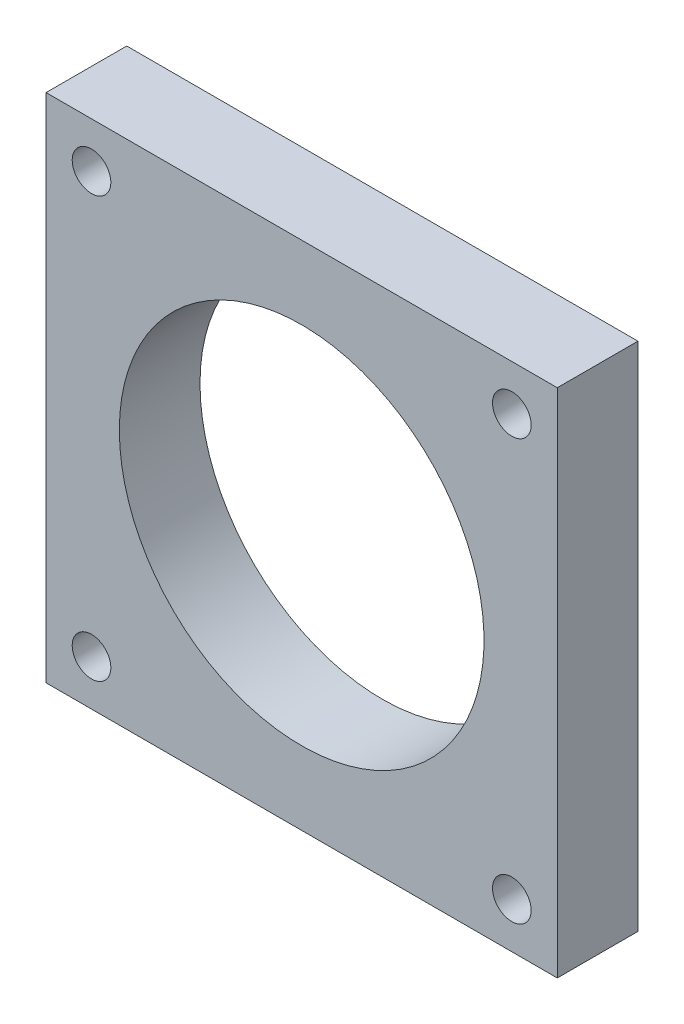
SolidWorks part; units mm, degrees
ref_plane "Front Plane" through (0, 0, 0) normal (0, 0, 1) x (1, 0, 0)
ref_plane "Top Plane" through (0, 0, 0) normal (0, 1, 0) x (1, 0, 0)
ref_plane "Right Plane" through (0, 0, 0) normal (1, 0, 0) x (0, 0, -1)
sketch "Sketch1" plane through (0, 0, 0) normal (0, 0, 1) x (1, 0, 0)
  line L1 (-22.5, -22.5) -> (22.5, -22.5)
  line L2 (-22.5, -22.5) -> (-22.5, 22.5)
  line L3 (-22.5, 22.5) -> (22.5, 22.5)
  line L4 (22.5, -22.5) -> (22.5, 22.5)
  line L5 (-22.5, -22.5) -> (22.5, 22.5) construction
  line L6 (-22.5, 22.5) -> (22.5, -22.5) construction
  circle A0 centre (0, 0) radius 16
  point P0 (0, 0)
  dimension "D3" = 32
  dimension "D1" = 45
  dimension "D2" = 45
extrude "Boss-Extrude1" add sketch "Sketch1" along normal blind 7.1
hole_wizard "M3x0.5 Tapped Hole1" positions "Sketch2" profile "Sketch3" tap size "M3x0.5" standard "ANSI Metric"
sketch "Sketch2" plane through (0, 0, 0) normal (0, 0, -1) x (-1, 0, 0)
  line L16 (-18.5, 18.5) -> (-18.5, -18.5)
  line L17 (-18.5, -18.5) -> (18.5, -18.5)
  line L18 (18.5, -18.5) -> (18.5, 18.5)
  line L19 (18.5, 18.5) -> (-18.5, 18.5)
  point P25 (-18.5, 18.5)
  point P26 (-18.5, -18.5)
  point P27 (18.5, -18.5)
  point P28 (18.5, 18.5)
sketch "Sketch3" plane through (18.5, 18.5, 0) normal (1, 0, 0) x (0, 1, 0)
  line L0 (0, 0) -> (0, 15.7511)
  line L1 (0, 15.7511) -> (1.25, 15)
  line L2 (1.25, 15) -> (1.25, 0)
  line L3 (1.25, 0) -> (0, 0)
  line L4 (0, 15.7511) -> (-1.25, 15) construction
  line L5 (0, -6.35) -> (0, 107.95) construction
  dimension "Tap Drill Dia." = 2.5
  dimension "Tap Drill Depth" = 15
  dimension "Drill Angle" = 118
cosmetic thread "Hole Thread1"
cosmetic thread "Hole Thread2"
cosmetic thread "Hole Thread3"
cosmetic thread "Hole Thread4"
hole_wizard "CBORE for M3 SHCS1" positions "Sketch4" profile "Sketch5" counterbore size "M3" standard "ANSI Metric"
sketch "Sketch4" plane through (0, 0, 0) normal (0, 0, -1) x (-1, 0, 0)
  point P0 (-18.5, 18.5)
  point P3 (18.5, 18.5)
  point P6 (18.5, -18.5)
  point P9 (-18.5, -18.5)
sketch "Sketch5" plane through (18.5, 18.5, 0) normal (1, 0, 0) x (0, 1, 0)
  line L0 (0, 0) -> (0, 8.1215)
  line L1 (0, 8.1215) -> (1.7, 7.1)
  line L2 (1.7, 7.1) -> (1.7, 3)
  line L3 (1.7, 3) -> (3.25, 3)
  line L4 (3.25, 3) -> (3.25, 0)
  line L5 (3.25, 0) -> (0, 0)
  line L6 (0, 8.1215) -> (-1.7, 7.1) construction
  line L7 (0, -6.35) -> (0, 107.95) construction
  dimension "Hole Dia." = 3.4
  dimension "Hole Depth" = 7.1
  dimension "C'Bore Dia." = 6.5
  dimension "C'Bore Depth" = 3
  dimension "Drill Angle" = 118
other "3D Printing Tolerance" face at (16, 0, 7.1) parameters "D1"=0.05
